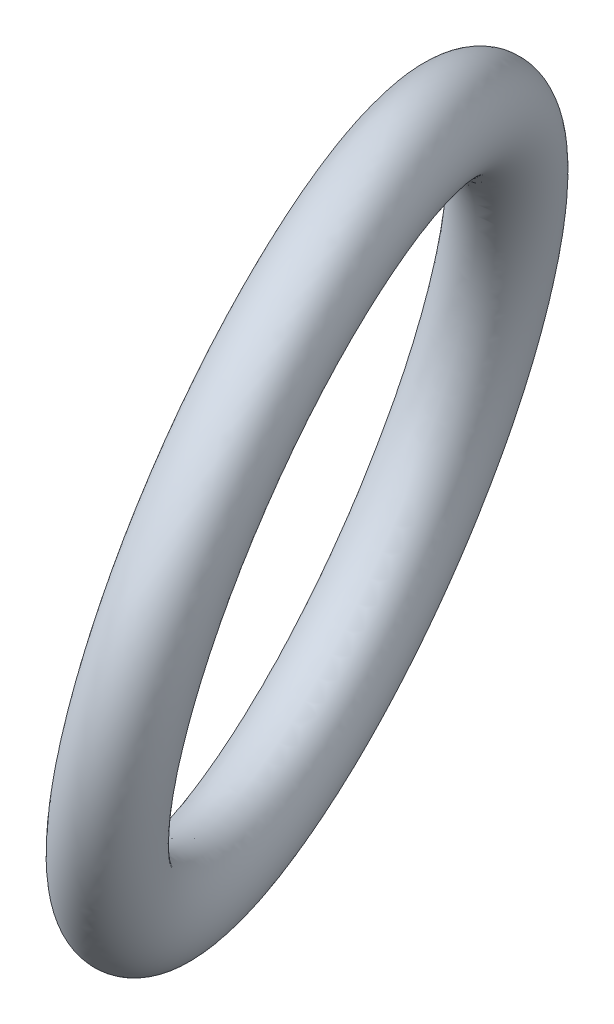
SolidWorks part; units mm, degrees
ref_plane "Front Plane" through (0, 0, 0) normal (0, 0, 1) x (1, 0, 0)
ref_plane "Top Plane" through (0, 0, 0) normal (0, 1, 0) x (1, 0, 0)
ref_plane "Right Plane" through (0, 0, 0) normal (1, 0, 0) x (0, 0, -1)
sketch "steering axle angle" plane through (0, 0, 0) normal (1, 0, 0) x (0, 0, -1)
  line L0 (0, 0) -> (381, 659.9114) construction
  line L1 (0, 0) -> (0, 5.9816) construction
  dimension "D1" = 30
  dimension "D2" = 762
sketch "Steering angle" plane through (0, 0, 0) normal (0, 1, 0) x (1, 0, 0)
  line L0 (0, 0) -> (-34.7492, 95.4728) construction
  line L1 (0, 0) -> (0, 381) construction
  line L2 (0, 0) -> (694.9849, -1909.4554) construction
  dimension "D1" = 20
  dimension "D2" = 101.6
  dimension "D3" = 2032
ref_plane "Plane of wheel" through (0, 0, 0) normal (-0.9219, 0.1937, 0.3355) x (0.3316, -0.0534, 0.9419)
sketch "wheel OD" plane through (0, 0, 0) normal (-0.9219, 0.1937, 0.3355) x (0.3316, -0.0534, 0.9419)
  line L0 (0, 0) -> (-394.1313, 652.1537) construction
  line L1 (0, 0) -> (-101.4492, -5.5342) construction
  line L2 (0, 0) -> (-154.4084, -8.0314) construction
  circle A0 centre (-154.4084, 255.4936) radius 263.525
  dimension "D1" = 527.05
  dimension "D2" = 154.4084
sketch "Sketch5" plane through (0, 0, 0) normal (0, 0, 1) x (1, 0, 0)
  line L0 (102.1026, 380.0034) -> (102.1026, 0) construction
  line L1 (102.1026, 0) -> (0, 0) construction
  line L2 (0, 0) -> (-102.1026, 0) construction
  line L3 (0, 0) -> (-34.7492, 0) construction
  line L4 (-102.1026, 0) -> (-102.1026, 137.0621) construction
  ellipse E0 centre (0, 258.5328) end of major axis (54.1931, 516.4253) minor radius 88.4234 construction
  dimension "D1" = 380.0034
  dimension "D2" = 137.0621
ref_plane "Planenormal to steering axle" through (0, 258.5328, -149.264) normal (0, 0.866, -0.5) x (1, 0, 0)
sketch "Steering axle input" plane through (0, 258.5328, -149.264) normal (0, 0.866, -0.5) x (1, 0, 0)
  line L0 (-102.1026, 242.9413) -> (102.1026, -242.9413) construction
  line L1 (-102.1026, 242.9413) -> (102.1026, -242.9413)
  line L2 (0, 0) -> (0, 361.5585) construction
  dimension "D1" = 22.796
sketch "Sketch8" plane through (0, 258.5328, -149.264) normal (0, 0.866, -0.5) x (1, 0, 0)
  line L0 (-102.1026, 242.9413) -> (102.1026, -242.9413) construction
  line L1 (-102.1026, 242.9413) -> (102.1026, -242.9413) construction
  line L2 (-47.0567, 228.1104) -> (-88.5418, 210.6751) construction
  line L3 (0, 0) -> (198.332, 83.3543) construction
  ellipse E0 centre (-88.5418, 210.6751) end of major axis (-102.1026, 242.9413) minor radius 31.2623
  ellipse E1 centre (88.5418, -210.6751) end of major axis (74.9811, -178.409) minor radius 31.2623 construction
  dimension "D1" = 45
  dimension "D2" = 35
revolve "Tire design" add sketch "Sketch8" angle 360 about L3
sketch "Vertical extent of tire" plane through (0, 0, 0) normal (0, 0, 1) x (1, 0, 0)
  line L0 (120.3758, 365.8253) -> (120.3758, 0) construction
  line L2 (0, 0) -> (694.9849, 0) construction
  line L3 (-120.3758, 151.2402) -> (-120.3758, 0) construction
  line L4 (-120.3758, 0) -> (0, 0) construction
  ellipse E0 centre (88.5418, 363.8703) end of major axis (56.7078, 361.9154) minor radius 17.1534 construction
  ellipse E1 centre (-88.5418, 153.1952) end of major axis (-56.7078, 155.1501) minor radius 17.1534
  ellipse E2 centre (-88.5418, 153.1952) end of major axis (-56.7078, 155.1501) minor radius 17.1534
  ellipse E3 centre (88.5418, 363.8703) end of major axis (120.3758, 365.8253) minor radius 17.1534
  dimension "D1" = 151.2402
  dimension "D3" = 120.3758
  dimension "D4" = 365.8253
  dimension "D5" = 120.3758
  dimension "D2" = 0
sketch "Sketch11" plane through (0, 0, 0) normal (0, 1, 0) x (1, 0, 0)
  line L0 (88.5418, -33.1861) -> (120.2896, -33.1861) construction
  line L1 (120.2896, -33.1861) -> (120.2896, 0) construction
  line L2 (56.6905, 0) -> (120.3932, 0) construction
  line L3 (120.2896, 0) -> (0, 0) construction
  line L4 (-88.5418, 331.714) -> (-120.2896, 331.714) construction
  line L5 (-120.2896, 331.714) -> (-120.2896, 0) construction
  line L6 (-120.3932, 0) -> (-56.6905, 0) construction
  line L7 (-120.2896, 0) -> (0, 0) construction
  ellipse E0 centre (-88.5418, 331.714) end of major axis (-59.291, 317.7312) minor radius 29.2274 construction
  ellipse E1 centre (88.5418, -33.1861) end of major axis (59.291, -19.2032) minor radius 29.2274 construction
  ellipse E2 centre (-88.5418, 331.714) end of major axis (-117.7927, 345.6968) minor radius 29.2274
  ellipse E3 centre (88.5418, -33.1861) end of major axis (59.291, -19.2032) minor radius 29.2274
  dimension "D1" = 120.2896
  dimension "D2" = 120.2896
  dimension "D3" = 33.1861
  dimension "D4" = 331.714
